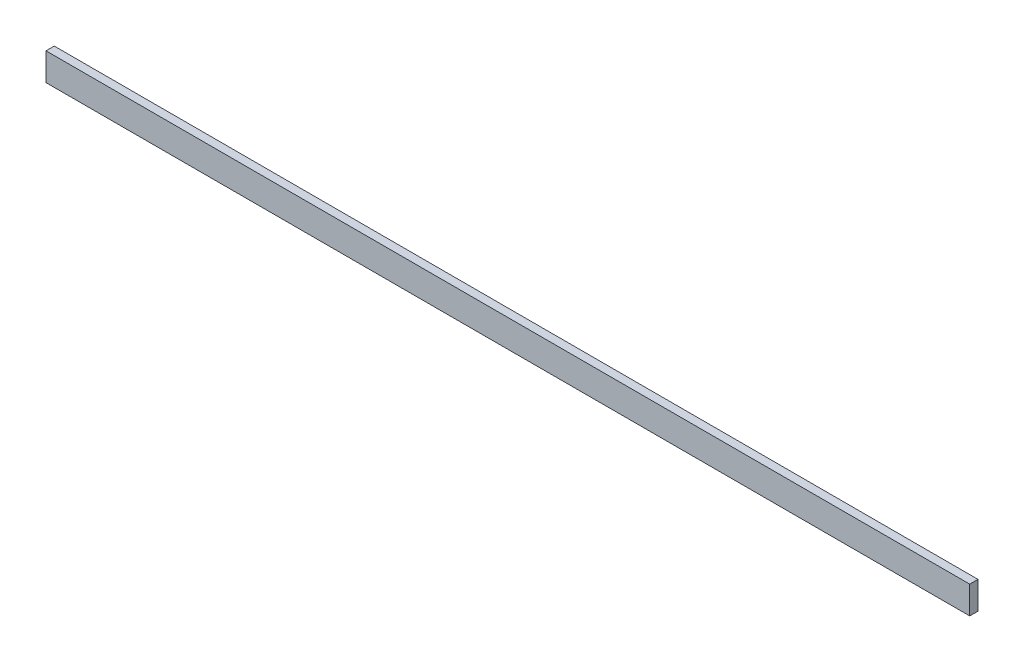
SolidWorks part; units mm, degrees
ref_plane "Front Plane" through (0, 0, 0) normal (0, 0, 1) x (1, 0, 0)
ref_plane "Top Plane" through (0, 0, 0) normal (0, 1, 0) x (1, 0, 0)
ref_plane "Right Plane" through (0, 0, 0) normal (1, 0, 0) x (0, 0, -1)
sketch "Sketch1" plane through (0, 0, 0) normal (0, 0, 1) x (1, 0, 0)
  line L1 (0, 0) -> (335, 0)
  line L2 (0, 0) -> (0, -10)
  line L3 (0, -10) -> (335, -10)
  line L4 (335, 0) -> (335, -10)
  dimension "D1" = 10
  dimension "D2" = 335
extrude "Boss-Extrude1" add sketch "Sketch1" along normal blind 3
